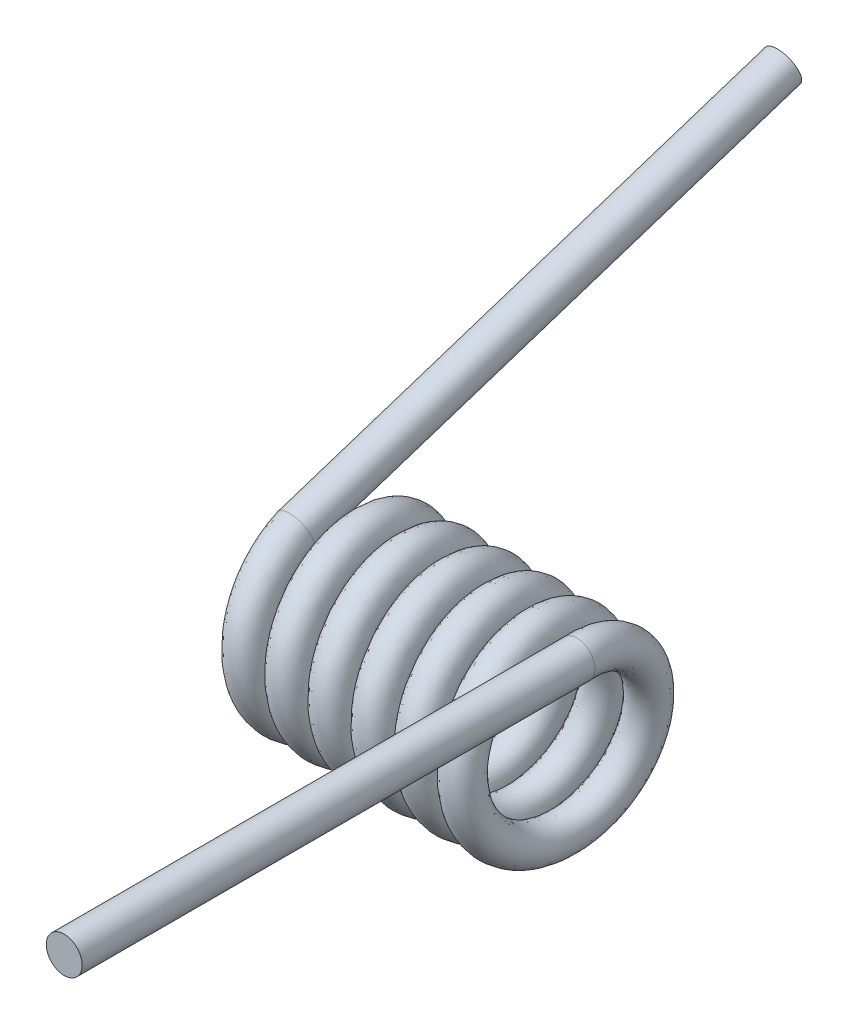
SolidWorks part; units mm, degrees
ref_plane "Front Plane" through (0, 0, 0) normal (0, 0, 1) x (1, 0, 0)
ref_plane "Top Plane" through (0, 0, 0) normal (0, 1, 0) x (1, 0, 0)
ref_plane "Right Plane" through (0, 0, 0) normal (1, 0, 0) x (0, 0, -1)
sketch "coil diameter" plane through (0, 0, 0) normal (1, 0, 0) x (0, 0, -1)
  circle A0 centre (0, 0) radius 2.032
  dimension "D1" = 4.064
curve "Helix/Spiral1" pitch 1.0672 height 6.35 turns 5.95
sketch "Sketch2" plane through (0, 0, 0) normal (0, 0, 1) x (1, 0, 0)
  circle A0 centre (0, 2.032) radius 0.4445
  spline S0 degree 3 poles (0, 2.032) (-0.0221, 2.032) (-0.0669, 1.9257) (-0.1337, 1.472) (-0.2005, 0.7932) (-0.2674, -0.0069) (-0.3342, -0.8059) (-0.4011, -1.4817) (-0.4679, -1.931) (-0.5347, -2.0851) (-0.6016, -1.9204) (-0.6684, -1.4622) (-0.7353, -0.7804) (-0.8021, 0.0207) (-0.8689, 0.8186) (-0.9358, 1.4914) (-1.0026, 1.9362) (-1.0695, 2.0849) (-1.1363, 1.915) (-1.2032, 1.4523) (-1.27, 0.7676) (-1.3368, -0.0345) (-1.4037, -0.8313) (-1.4705, -1.501) (-1.5374, -1.9412) (-1.6042, -2.0847) (-1.6711, -1.9095) (-1.7379, -1.4424) (-1.8047, -0.7547) (-1.8716, 0.0483) (-1.9384, 0.8439) (-2.0053, 1.5105) (-2.0721, 1.9462) (-2.1389, 2.0844) (-2.2058, 1.9039) (-2.2726, 1.4324) (-2.3395, 0.7419) (-2.4063, -0.062) (-2.4732, -0.8565) (-2.54, -1.52) (-2.6068, -1.9511) (-2.6737, -2.084) (-2.7405, -1.8983) (-2.8074, -1.4223) (-2.8742, -0.729) (-2.9411, 0.0758) (-3.0079, 0.869) (-3.0747, 1.5294) (-3.1416, 1.9559) (-3.2084, 2.0835) (-3.2753, 1.8925) (-3.3421, 1.4122) (-3.4089, 0.716) (-3.4758, -0.0896) (-3.5426, -0.8816) (-3.6095, -1.5387) (-3.6763, -1.9607) (-3.7432, -2.0829) (-3.81, -1.8867) (-3.8768, -1.402) (-3.9437, -0.7031) (-4.0105, 0.1034) (-4.0774, 0.894) (-4.1442, 1.548) (-4.2111, 1.9653) (-4.2779, 2.0822) (-4.3447, 1.8808) (-4.4116, 1.3918) (-4.4784, 0.6901) (-4.5453, -0.1172) (-4.6121, -0.9065) (-4.6789, -1.5572) (-4.7458, -1.9699) (-4.8126, -2.0814) (-4.8795, -1.8748) (-4.9463, -1.3815) (-5.0132, -0.677) (-5.08, 0.1309) (-5.1468, 0.9189) (-5.2137, 1.5664) (-5.2805, 1.9744) (-5.3474, 2.0806) (-5.4142, 1.8687) (-5.4811, 1.3711) (-5.5479, 0.664) (-5.6147, -0.1447) (-5.6816, -0.9312) (-5.7484, -1.5754) (-5.8153, -1.9788) (-5.8821, -2.0796) (-5.9489, -1.8625) (-6.0158, -1.3607) (-6.0826, -0.6509) (-6.1495, 0.1584) (-6.2163, 0.9436) (-6.2831, 1.5842) (-6.3279, 1.8507) (-6.35, 1.9325) knots 0 0 0 0 0.010526 0.021053 0.031579 0.042105 0.052632 0.063158 0.073684 0.084211 0.094737 0.105263 0.115789 0.126316 0.136842 0.147368 0.157895 0.168421 0.178947 0.189474 0.2 0.210526 0.221053 0.231579 0.242105 0.252632 0.263158 0.273684 0.284211 0.294737 0.305263 0.315789 0.326316 0.336842 0.347368 0.357895 0.368421 0.378947 0.389474 0.4 0.410526 0.421053 0.431579 0.442105 0.452632 0.463158 0.473684 0.484211 0.494737 0.505263 0.515789 0.526316 0.536842 0.547368 0.557895 0.568421 0.578947 0.589474 0.6 0.610526 0.621053 0.631579 0.642105 0.652632 0.663158 0.673684 0.684211 0.694737 0.705263 0.715789 0.726316 0.736842 0.747368 0.757895 0.768421 0.778947 0.789474 0.8 0.810526 0.821053 0.831579 0.842105 0.852632 0.863158 0.873684 0.884211 0.894737 0.905263 0.915789 0.926316 0.936842 0.947368 0.957895 0.968421 0.978947 0.989474 1 1 1 1 construction
  dimension "D1" = 0.889
sweep "spring main coil" add profiles "Sketch2" path "Helix/Spiral1"
sketch "Sketch3" plane through (0, 0, 0) normal (0, 0, 1) x (1, 0, 0)
  circle A1 centre (0, 2.032) radius 0.4445
  circle A2 centre (0, 2.032) radius 0.4445
  point P3 (0.4445, 2.032)
  dimension "D1" = 0
extrude "front leg" add sketch "Sketch3" along normal blind 12.7
sketch "Sketch4" plane through (0, 0, 0) normal (0, 0.309, -0.9511) x (-1, 0, 0)
  circle A1 centre (6.3503, 2.032) radius 0.4445
  circle A2 centre (6.3503, 2.032) radius 0.4445
  point P3 (6.7948, 2.032)
  dimension "D1" = 0
extrude "rear leg" add sketch "Sketch4" along normal blind 12.7
ref_plane "right-side plane" through (0.4445, 0, 0) normal (1, 0, 0) x (0, 0, -1)
ref_plane "left-side plane" through (-6.7948, 0, 0) normal (1, 0, 0) x (0, 0, -1)
ref_plane "center plane" through (-3.1752, 0, 0) normal (1, 0, 0) x (0, 0, -1)
